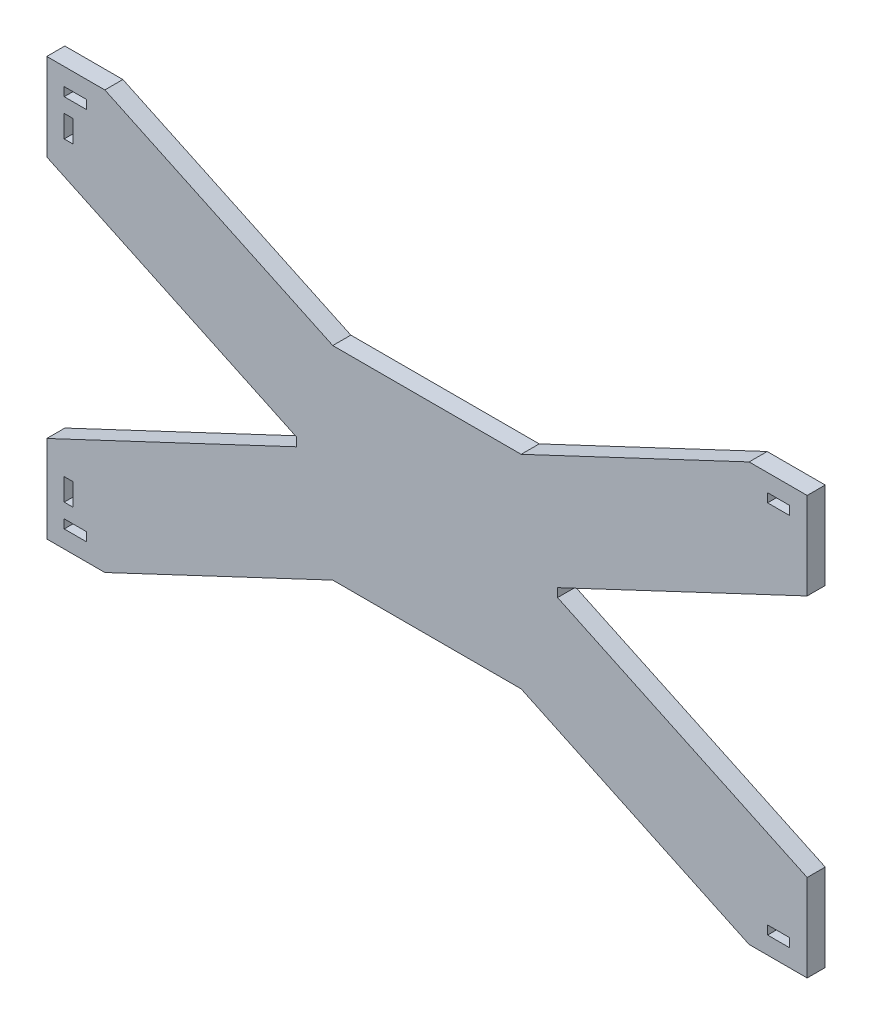
SolidWorks part; units mm, degrees
ref_plane "정면" through (0, 0, 0) normal (0, 0, 1) x (1, 0, 0)
ref_plane "윗면" through (0, 0, 0) normal (0, 1, 0) x (1, 0, 0)
ref_plane "우측면" through (0, 0, 0) normal (1, 0, 0) x (0, 0, -1)
sketch "Sketch1" plane through (0, 0, 0) normal (0, 0, 1) x (1, 0, 0)
  line L0 (0.7314, 35.6412) -> (0.7314, -36.3588) construction
  line L1 (-64.7686, -36.3588) -> (-54.7686, -36.3588)
  line L2 (-64.7686, -36.3588) -> (-64.7686, -21.3588)
  line L3 (-64.7686, 35.6412) -> (-54.7686, 35.6412)
  line L4 (66.2314, -36.3588) -> (66.2314, -21.3588)
  line L5 (-64.7686, -0.3588) -> (-21.7686, -0.3588) construction
  line L6 (0.7314, -0.3588) -> (-21.7686, -0.3588) construction
  line L7 (-21.7686, -0.3588) -> (-21.7686, -1.1026) construction
  line L8 (-15.4967, 17.1412) -> (16.9594, 17.1412)
  line L9 (-15.4967, -17.8588) -> (16.9594, -17.8588)
  line L10 (-21.7686, -1.1026) -> (-21.7686, 0.385)
  line L11 (0.7314, -0.3588) -> (66.2314, -0.3588) construction
  line L12 (56.2314, 35.6412) -> (66.2314, 35.6412)
  line L13 (23.2314, -0.3588) -> (23.2314, -1.1026) construction
  line L14 (23.2314, -1.1026) -> (23.2314, 0.385)
  line L15 (66.2314, 20.6412) -> (66.2314, 35.6412)
  line L16 (56.2314, -36.3588) -> (66.2314, -36.3588)
  line L17 (66.2314, 35.6412) -> (56.2314, 35.6412) construction
  line L18 (56.2314, -36.3588) -> (16.9594, -17.8588)
  line L19 (-64.7686, -21.3588) -> (-21.7686, -1.1026)
  line L20 (-54.7686, -36.3588) -> (-15.4967, -17.8588)
  line L21 (66.2314, -21.3588) -> (23.2314, -1.1026)
  line L22 (-15.4967, 17.1412) -> (-54.7686, 35.6412)
  line L23 (16.9594, 17.1412) -> (56.2314, 35.6412)
  line L24 (23.2314, 0.385) -> (66.2314, 20.6412)
  line L25 (-21.7686, 0.385) -> (-64.7686, 20.6412)
  line L26 (-64.7686, 20.6412) -> (-64.7686, 35.6412)
  line L27 (-64.7686, -36.3588) -> (-64.7686, -33.3588) construction
  line L28 (-60.2586, 28.6412) -> (-61.7686, 28.6412)
  line L29 (-60.2586, 24.8312) -> (-60.2586, 28.6412)
  line L30 (-61.7686, -29.3588) -> (-61.7686, -25.5488)
  line L31 (-61.7686, -25.5488) -> (-60.2586, -25.5488)
  line L32 (-60.2586, -25.5488) -> (-60.2586, -29.3588)
  line L33 (-60.2586, -29.3588) -> (-61.7686, -29.3588)
  line L34 (-61.7686, 24.8312) -> (-60.2586, 24.8312)
  line L35 (-61.7686, 28.6412) -> (-61.7686, 24.8312)
  line L36 (-57.9586, 32.6412) -> (-57.9586, 31.1312)
  line L37 (-61.7686, 31.1312) -> (-57.9586, 31.1312)
  line L38 (-61.7686, -33.3588) -> (-57.9586, -33.3588)
  line L39 (-61.7686, -33.3588) -> (-61.7686, -31.8488)
  line L40 (-61.7686, -31.8488) -> (-57.9586, -31.8488)
  line L41 (-57.9586, -33.3588) -> (-57.9586, -31.8488)
  line L42 (-61.7686, 32.6412) -> (-61.7686, 31.1312)
  line L43 (-61.7686, 32.6412) -> (-57.9586, 32.6412)
  line L44 (63.2314, 32.6412) -> (59.4214, 32.6412)
  line L45 (63.2314, 32.6412) -> (63.2314, 31.1312)
  line L46 (63.2314, 31.1312) -> (59.4214, 31.1312)
  line L47 (59.4214, 32.6412) -> (59.4214, 31.1312)
  line L48 (59.4214, -33.3588) -> (59.4214, -31.8488)
  line L49 (63.2314, -31.8488) -> (59.4214, -31.8488)
  line L50 (63.2314, -33.3588) -> (63.2314, -31.8488)
  line L51 (63.2314, -33.3588) -> (59.4214, -33.3588)
  dimension "D1" = 7
  dimension "D2" = 131
  dimension "D3" = 72
extrude "Boss-Extrude1" add sketch "Sketch1" along normal blind 3.1115
